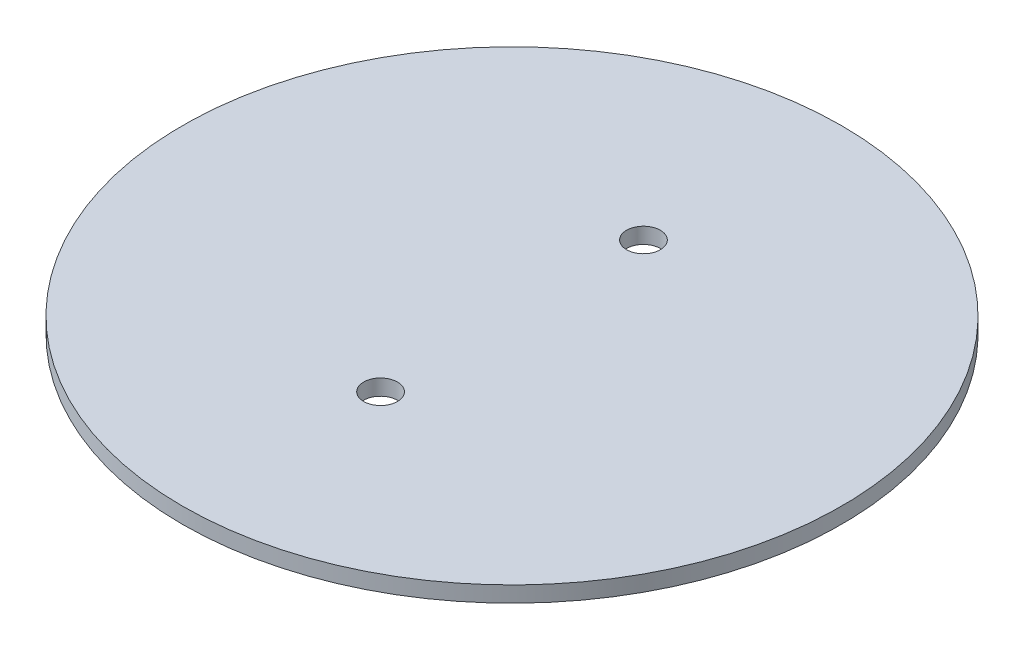
SolidWorks part; units mm, degrees
ref_plane "Front Plane" through (0, 0, 0) normal (0, 0, 1) x (1, 0, 0)
ref_plane "Top Plane" through (0, 0, 0) normal (0, 1, 0) x (1, 0, 0)
ref_plane "Right Plane" through (0, 0, 0) normal (1, 0, 0) x (0, 0, -1)
sketch "Sketch1" plane through (0, 0, 0) normal (0, 1, 0) x (1, 0, 0)
  circle A0 centre (0, 0) radius 62.5
  dimension "D1" = 125
extrude "Boss-Extrude1" add sketch "Sketch1" along normal blind 3 contours A0
sketch "Sketch2" plane through (0, 3, 0) normal (0, 1, 0) x (1, 0, 0)
  line L0 (-1.65, 0) -> (1.65, 0) construction
  circle A0 centre (0, 24.9283) radius 3.2035
  circle A1 centre (0, -24.9283) radius 3.2035
extrude "Cut-Extrude1" cut sketch "Sketch2" against normal through all
